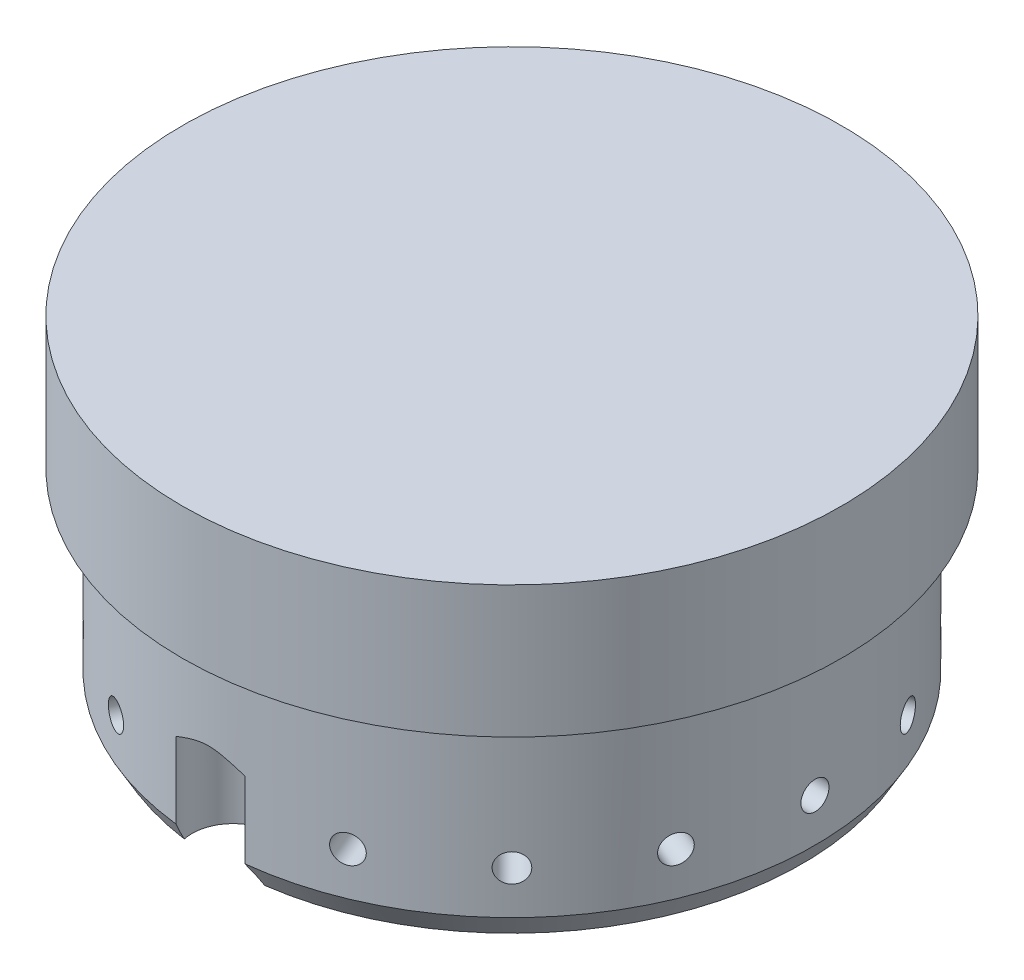
SolidWorks part; units mm, degrees
material "6061-T6 (SS)"
ref_plane "Front Plane" through (0, 0, 0) normal (0, 0, 1) x (1, 0, 0)
ref_plane "Top Plane" through (0, 0, 0) normal (0, 1, 0) x (1, 0, 0)
ref_plane "Right Plane" through (0, 0, 0) normal (1, 0, 0) x (0, 0, -1)
ref_axis "Center Axis" through (0, 0, 0) along (0, 1, 0)
sketch "Sketch1" plane through (0, 0, 0) normal (0, 0, 1) x (1, 0, 0)
  line L0 (0, 0) -> (-58.4454, 0)
  line L1 (-58.4454, 0) -> (-58.4454, 38.1)
  line L2 (-58.4454, 38.1) -> (-63.5, 38.1)
  line L3 (-63.5, 38.1) -> (-63.5, 63.5)
  line L4 (-63.5, 63.5) -> (0, 63.5)
  line L5 (0, 63.5) -> (0, 0)
  dimension "D1" = 58.4454
  dimension "D2" = 63.5
  dimension "D3" = 38.1
revolve "Revolve1" add sketch "Sketch1" angle 360 about L5
ref_plane "Tap Reference Plane" through (0, 0, 58.4454) normal (0, 0, 1) x (1, 0, 0)
sketch "Hole Reference" plane through (0, 0, 58.4454) normal (0, 0, 1) x (1, 0, 0)
  line L0 (0, 0) -> (0, 12.7)
  point P4 (0, 12.7)
hole_wizard "1/4-28 Tap" positions "Sketch11" profile "Sketch13" hole size "1/4-28" standard "ANSI Inch"
sketch "Sketch11" plane through (0, 0, 58.4454) normal (0, 0, 1) x (1, 0, 0)
  point P0 (0, 12.7)
sketch "Sketch13" plane through (0, 12.7, 58.4454) normal (1, 0, 0) x (0, -1, 0)
  line L0 (0, 0) -> (0, 20.6754)
  line L1 (0, 20.6754) -> (2.7051, 19.05)
  line L2 (2.7051, 19.05) -> (2.7051, 0)
  line L5 (2.7051, 0) -> (0, 0)
  line L10 (0, 20.6754) -> (-2.7051, 19.05) construction
  line L11 (0, -6.35) -> (0, 107.95) construction
  dimension "Hole Dia." = 5.4102
  dimension "Hole Depth" = 19.05
  dimension "Drill Angle" = 118
pattern_circular "Tap Pattern" count 16 over 360 about axis through (0, 0, 0) along (0, 1, 0) of "1/4-28 Tap"
chamfer "Chamfer1" distance 2.54 angle 60 1 edges at (0, 0, 58.4454)
sketch "Sketch14" plane through (0, 0, 0) normal (0, -1, 0) x (1, 0, 0)
  circle A2 centre (0, 0) radius 58.4454 construction
  point P0 (0, 53.6829)
  point P1 (0, -53.6829)
  dimension "D1" = 4.7625
  dimension "D2" = 4.7625
hole_wizard "5/8 (0.625) Diameter Hole1" positions "Sketch15" profile "Sketch16" hole size "5/8" standard "ANSI Inch"
sketch "Sketch15" plane through (0, 0, 0) normal (0, -1, 0) x (-1, 0, 0)
  point P0 (0, -53.6829)
  point P3 (0, 53.6829)
sketch "Sketch16" plane through (0, 0, 53.6829) normal (1, 0, 0) x (0, 0, -1)
  line L0 (0, 0) -> (0, 23.8193)
  line L1 (0, 23.8193) -> (7.9375, 19.05)
  line L2 (7.9375, 19.05) -> (7.9375, 0)
  line L5 (7.9375, 0) -> (0, 0)
  line L10 (0, 23.8193) -> (-7.9375, 19.05) construction
  line L11 (0, -6.35) -> (0, 107.95) construction
  dimension "Hole Dia." = 15.875
  dimension "Hole Depth" = 19.05
  dimension "Drill Angle" = 118
